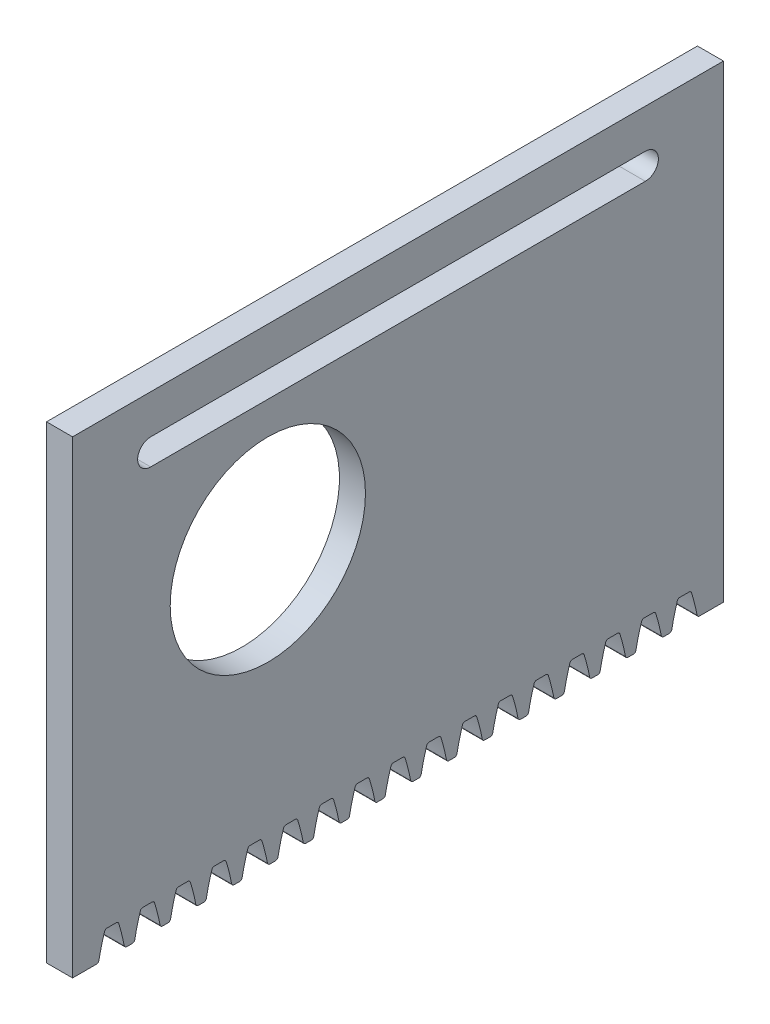
SolidWorks part; units mm, degrees
ref_plane "Front Plane" through (0, 0, 0) normal (0, 0, 1) x (1, 0, 0)
ref_plane "Top Plane" through (0, 0, 0) normal (0, 1, 0) x (1, 0, 0)
ref_plane "Right Plane" through (0, 0, 0) normal (1, 0, 0) x (0, 0, -1)
sketch "Sketch1" plane through (0, 0, 0) normal (1, 0, 0) x (0, 0, -1)
  line L0 (-12.4352, -6) -> (20, -6)
  line L5 (-12.4352, 30) -> (-12.4352, -6)
  line L7 (37.5648, 30) -> (37.5648, -6)
  line L8 (37.5648, -6) -> (20, -6)
  line L9 (-12.4352, 30) -> (37.5648, 30)
  dimension "D1" = 36
  dimension "D2" = 50
extrude "Boss-Extrude1" add sketch "Sketch1" along normal blind 2
sketch "Sketch3" plane through (0, 0, 0) normal (-1, 0, 0) x (0, 0, 1)
  line L1 (-13.0648, -4) -> (-12.0648, -4)
  line L3 (-12.5648, -6) -> (-12.5648, 30) construction
  line L4 (12.4352, -6) -> (-37.5648, -6) construction
  line L5 (-13.5648, -6) -> (-11.5648, -6)
  line L6 (12.4352, 30) -> (-37.5648, 30) construction
  arc A0 (-13.0648, -4) -> (-13.5648, -6) centre (1.203, -8.6294) ccw
  arc A1 (-12.0648, -4) -> (-11.5648, -6) centre (-26.3325, -8.6294) cw
  point P7 (-12.5648, -4)
  dimension "D1" = 15
  dimension "D6" = 15
  dimension "D2" = 2
  dimension "D3" = 1
  dimension "D4" = 2
  dimension "D5" = 1
extrude "Cut-Extrude2" cut sketch "Sketch3" against normal through all
fillet "Fillet1" radius 0.2 4 edges at (1, -6, -13.5648) (1, -4, -13.0648) (1, -4, -12.0648) (1, -6, -11.5648)
pattern_linear "LPattern1" count 9 spacing 2.75 along (0, 0, 1) count 9 spacing 2.75 along (0, 0, -1) of "Cut-Extrude2", "Fillet1"
sketch "Sketch4" plane through (0, 0, 0) normal (-1, 0, 0) x (0, 0, 1)
  line L2 (12.4352, 30) -> (-37.5648, 30) construction
  line L3 (12.4352, 30) -> (12.4352, -6) construction
  circle A0 centre (-2.5648, 15) radius 7.5
  dimension "D1" = 15
  dimension "D2" = 15
  dimension "D3" = 15
extrude "Cut-Extrude3" cut sketch "Sketch4" against normal blind 10
sketch "Sketch5" plane through (0, 0, 0) normal (-1, 0, 0) x (0, 0, 1)
  line L0 (-31.5648, 26) -> (6.4352, 26) construction
  line L1 (-31.5648, 27) -> (6.4352, 27)
  line L2 (-31.5648, 25) -> (6.4352, 25)
  line L4 (12.4352, 30) -> (-37.5648, 30) construction
  line L5 (-37.5648, 30) -> (-37.5648, -6) construction
  line L6 (12.4352, 30) -> (12.4352, -6) construction
  arc A0 (-31.5648, 27) -> (-31.5648, 25) centre (-31.5648, 26) ccw
  arc A1 (6.4352, 25) -> (6.4352, 27) centre (6.4352, 26) ccw
  point P2 (-12.5648, 26)
  dimension "D1" = 4
  dimension "D2" = 6
  dimension "D3" = 6
  dimension "D4" = 2
extrude "Cut-Extrude4" cut sketch "Sketch5" against normal blind 10
